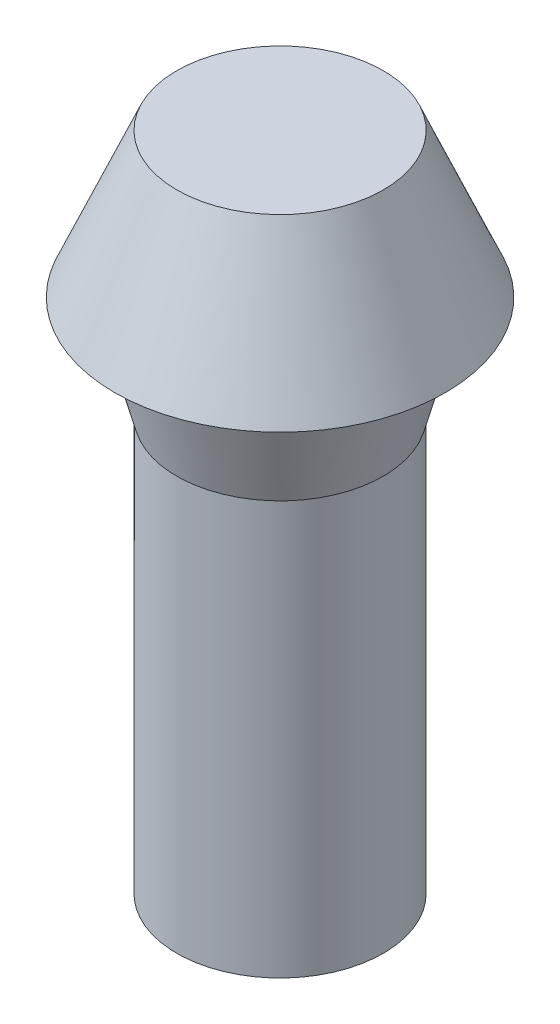
SolidWorks part; units mm, degrees
ref_plane "Front Plane" through (0, 0, 0) normal (0, 0, 1) x (1, 0, 0)
ref_plane "Top Plane" through (0, 0, 0) normal (0, 1, 0) x (1, 0, 0)
ref_plane "Right Plane" through (0, 0, 0) normal (1, 0, 0) x (0, 0, -1)
sketch "Sketch1" plane through (0, 0, 0) normal (0, 1, 0) x (1, 0, 0)
  circle A0 centre (0, 0) radius 8
  dimension "D1" = 16
ref_plane "Plane1" through (0, 7, 0) normal (0, 1, 0) x (1, 0, 0)
sketch "Sketch3" plane through (0, 7, 0) normal (0, 1, 0) x (1, 0, 0)
  circle A0 centre (0, 0) radius 5
  dimension "D1" = 10
loft "Loft1" add profiles "Sketch3", "Sketch1"
ref_plane "Plane2" through (0, -5, 0) normal (0, -1, 0) x (-1, 0, 0)
sketch "Sketch4" plane through (0, -5, 0) normal (0, -1, 0) x (-1, 0, 0)
  circle A0 centre (0, 0) radius 5 construction
  circle A1 centre (0, 0) radius 5
extrude "Boss-Extrude1" add sketch "Sketch4" against normal blind 5 draft 15 draft outward yes
sketch "Sketch5" plane through (0, -5, 0) normal (0, -1, 0) x (-1, 0, 0)
  circle A0 centre (0, 0) radius 5 construction
  circle A1 centre (0, 0) radius 5
extrude "Boss-Extrude2" add sketch "Sketch5" along normal blind 20
